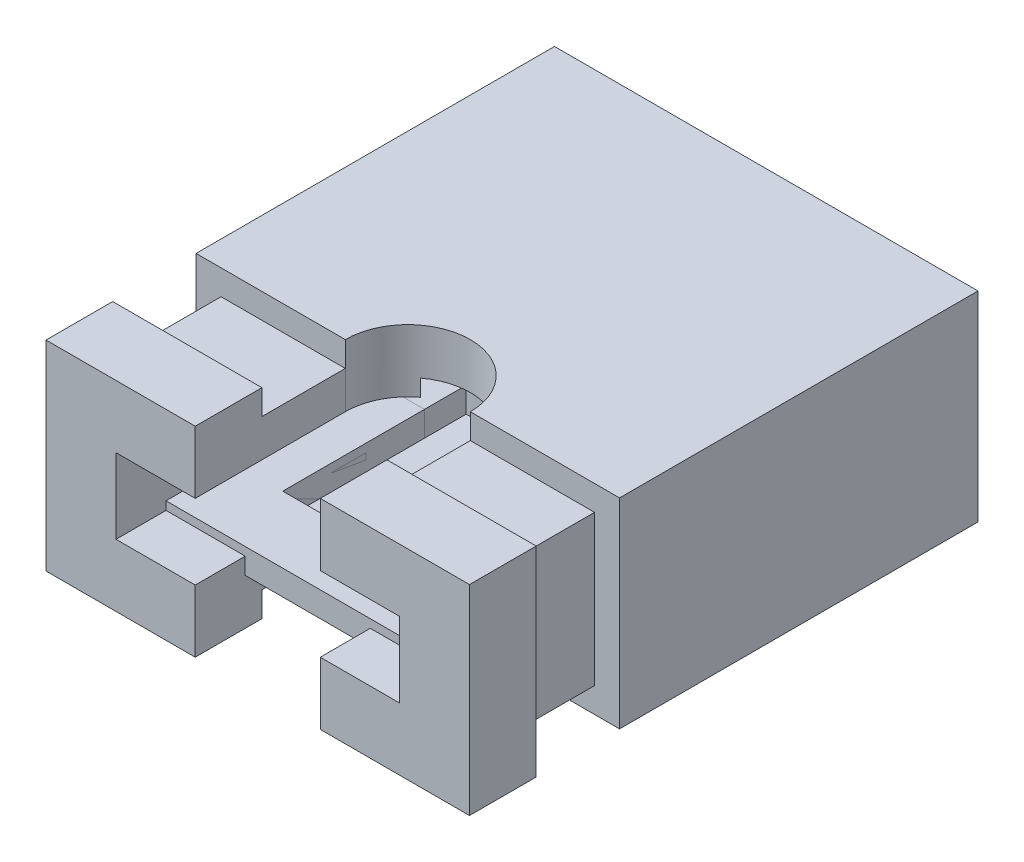
SolidWorks part; units mm, degrees
ref_plane "Front Plane" through (0, 0, 0) normal (0, 0, 1) x (1, 0, 0)
ref_plane "Top Plane" through (0, 0, 0) normal (0, 1, 0) x (1, 0, 0)
ref_plane "Right Plane" through (0, 0, 0) normal (1, 0, 0) x (0, 0, -1)
sketch "Sketch1" plane through (0, 0, 0) normal (0, 0, 1) x (1, 0, 0)
  line L0 (-1.9, 0.65) -> (-1.9, -0.65)
  line L1 (2.54, -1.2) -> (2.54, 1.2)
  line L2 (2.54, 1.2) -> (-2.54, 1.2)
  line L3 (-2.54, 1.2) -> (-2.54, -1.2)
  line L4 (-2.54, -1.2) -> (2.54, -1.2)
  line L5 (-1.9, -0.65) -> (1.9, -0.65)
  line L6 (1.9, 0.65) -> (-1.9, 0.65)
  line L7 (1.9, -0.65) -> (1.9, 0.65)
extrude "Boss-Extrude1" add sketch "Sketch1" along normal blind 4.3
sketch "Sketch3" plane through (0, 1.2, 0) normal (0, 1, 0) x (1, 0, 0)
  line L0 (2.54, -4.3) -> (-2.54, -4.3) construction
  circle A0 centre (0, -4.3) radius 0.75
extrude "Cut-Extrude2" cut sketch "Sketch3" against normal through all
sketch "Sketch6" plane through (0, 0, 4.3) normal (0, 0, 1) x (1, 0, 0)
  line L2 (-0.75, 0.9) -> (-0.75, 0.65)
  line L3 (-0.75, 0.65) -> (-1.9, 0.65)
  line L4 (-2.24, 0.9) -> (-2.24, -1.2)
  line L5 (-0.75, 0.9) -> (-2.24, 0.9)
  line L6 (-2.24, 0.9) -> (-2.24, -0.9)
  line L7 (-0.75, 0.9) -> (-2.24, 0.9)
  line L8 (-1.9, 0.65) -> (-1.9, -0.65)
  line L9 (-1.9, -0.65) -> (-0.75, -0.65)
  line L10 (-0.75, -0.65) -> (-0.75, -0.9)
  line L13 (0, 1.726) -> (0, -1.726) construction
  line L14 (-2.54, -0.9) -> (-0.75, -0.9)
  line L15 (-2.24, -0.9) -> (-0.75, -0.9)
  line L16 (2.24, 0.9) -> (2.24, -0.9)
  line L17 (2.24, -0.9) -> (0.75, -0.9)
  line L18 (1.9, -0.65) -> (0.75, -0.65)
  line L19 (1.9, 0.65) -> (1.9, -0.65)
  line L20 (0.75, 0.65) -> (1.9, 0.65)
  line L21 (0.75, 0.9) -> (0.75, 0.65)
  line L22 (0.75, 0.9) -> (2.24, 0.9)
  line L23 (0.75, -0.65) -> (0.75, -0.9)
  point P18 (0, 0)
  dimension "D1" = 0.3
  dimension "D2" = 0.3
extrude "Boss-Extrude2" add sketch "Sketch6" along normal blind 1
sketch "Sketch7" plane through (0, 0, 5.3) normal (0, 0, 1) x (1, 0, 0)
  line L8 (-0.75, 1.2) -> (-0.75, 0.9) construction
  line L9 (-0.75, 1.2) -> (-0.75, 0.9)
  line L10 (-0.75, -0.65) -> (-1.9, -0.65) construction
  line L11 (-1.9, -0.65) -> (-1.9, 0.65) construction
  line L12 (-1.9, 0.65) -> (-0.75, 0.65) construction
  line L13 (-0.75, -0.65) -> (-1.9, -0.65)
  line L14 (-1.9, -0.65) -> (-1.9, 0.65)
  line L15 (-1.9, 0.65) -> (-0.75, 0.65)
  line L16 (-0.45, -0.35) -> (-1.6, -0.35)
  line L17 (-0.45, -1.2) -> (-0.45, -0.35)
  line L18 (-2.54, -1.2) -> (-0.45, -1.2)
  line L19 (-2.54, 1.2) -> (-2.54, -1.2)
  line L20 (-1.6, -0.35) -> (-1.6, 0.35)
  line L21 (-0.45, 0.35) -> (-0.45, 1.2)
  line L22 (-0.45, 1.2) -> (-2.54, 1.2)
  line L23 (-1.6, 0.35) -> (-0.45, 0.35)
  line L26 (-2.54, -1.2) -> (-0.75, -1.2)
  line L27 (-2.54, 1.2) -> (-2.54, -1.2)
  line L30 (-0.75, 1.2) -> (-2.54, 1.2)
  line L33 (-0.75, -0.9) -> (-0.75, -1.2) construction
  line L35 (-0.75, -0.9) -> (-0.75, -1.2)
  line L36 (-0.75, -0.9) -> (-0.75, -0.65) construction
  line L37 (-0.75, -0.9) -> (-0.75, -0.65)
  line L39 (0.75, -0.9) -> (0.75, -1.2)
  line L40 (0.75, 1.2) -> (0.75, 0.9)
  line L41 (0.75, -0.9) -> (0.75, -0.65)
  line L42 (0.75, 1.2) -> (2.54, 1.2)
  line L43 (2.54, 1.2) -> (2.54, -1.2)
  line L44 (2.54, -1.2) -> (0.75, -1.2)
  line L45 (1.9, 0.65) -> (0.75, 0.65)
  line L46 (1.9, -0.65) -> (1.9, 0.65)
  line L47 (0.75, -0.65) -> (1.9, -0.65)
  line L48 (0.75, 0.9) -> (0.75, 0.65) construction
  line L49 (0.75, 0.9) -> (0.75, 0.65)
  line L50 (-0.75, 0.65) -> (-0.75, 0.9) construction
  line L51 (-0.75, 0.65) -> (-0.75, 0.9)
  point P20 (0, 0)
  dimension "D1" = 0.3
extrude "Boss-Extrude3" add sketch "Sketch7" along normal blind 0.8
sketch "Sketch9" plane through (0, 0, 6.1) normal (0, 0, 1) x (1, 0, 0)
  line L0 (0.75, 0.65) -> (1.9, 0.65) construction
  line L1 (1.9, 0.65) -> (1.9, -0.65) construction
  line L2 (1.9, -0.65) -> (0.75, -0.65) construction
  line L3 (-0.75, -0.65) -> (-1.9, -0.65) construction
  line L4 (-1.9, -0.65) -> (-1.9, 0.65) construction
  line L5 (-1.9, 0.65) -> (-0.75, 0.65) construction
  line L18 (0.75, 0.65) -> (1.9, 0.65)
  line L19 (1.9, 0.65) -> (1.9, -0.65)
  line L20 (1.9, -0.65) -> (0.75, -0.65)
  line L21 (-0.75, -0.65) -> (-1.9, -0.65)
  line L22 (-1.9, -0.65) -> (-1.9, 0.65)
  line L23 (-1.9, 0.65) -> (-0.75, 0.65)
  line L24 (-0.75, -0.45) -> (-1.7, -0.45)
  line L25 (-1.7, -0.45) -> (-1.7, 0.45)
  line L26 (-1.7, 0.45) -> (-0.75, 0.45)
  line L27 (0.75, 0.45) -> (1.7, 0.45)
  line L28 (1.7, 0.45) -> (1.7, -0.45)
  line L29 (1.7, -0.45) -> (0.75, -0.45)
  line L34 (-0.75, 0.65) -> (0.75, 0.65)
  line L35 (0.75, 0.45) -> (-0.75, 0.45)
  line L36 (-0.75, -0.45) -> (0.75, -0.45)
  line L37 (0.75, -0.65) -> (-0.75, -0.65)
  dimension "D1" = 0.2
extrude "Boss-Extrude4" add sketch "Sketch9" against normal blind 2.4
sketch "Sketch10" plane through (0, 0.65, 0) normal (0, 1, 0) x (1, 0, 0)
  line L0 (0.75, -6.1) -> (0.75, -4.3) construction
  line L1 (-0.75, -6.1) -> (-0.75, -4.3) construction
  line L2 (0.75, -6.1) -> (0.75, -4.3)
  line L3 (-0.75, -6.1) -> (-0.75, -4.3)
  line L4 (0.75, -6.1) -> (-0.75, -6.1) construction
  line L5 (0.75, -6.1) -> (-0.75, -6.1)
  arc A0 (0.75, -4.3) -> (0.45, -3.7) centre (0, -4.3) ccw construction
  arc A1 (-0.45, -3.7) -> (-0.75, -4.3) centre (0, -4.3) ccw construction
  arc A2 (0.45, -3.7) -> (-0.45, -3.7) centre (0, -4.3) ccw construction
  arc A3 (0.75, -4.3) -> (0.45, -3.7) centre (0, -4.3) ccw
  arc A4 (-0.45, -3.7) -> (-0.75, -4.3) centre (0, -4.3) ccw
  arc A5 (0.45, -3.7) -> (-0.45, -3.7) centre (0, -4.3) ccw
extrude "Cut-Extrude4" cut sketch "Sketch10" against normal through all
sketch "Sketch12" plane through (0, 0, 0) normal (0, 0, -1) x (-1, 0, 0)
  line L0 (1.9, 0.65) -> (1.9, -0.65) construction
  line L1 (1.9, -0.65) -> (-1.9, -0.65) construction
  line L2 (-1.9, -0.65) -> (-1.9, 0.65) construction
  line L3 (1.9, 0.65) -> (1.9, -0.65)
  line L4 (1.9, -0.65) -> (-1.9, -0.65)
  line L5 (-1.9, -0.65) -> (-1.9, 0.65)
  line L6 (1.6, 0.65) -> (1.6, -0.35)
  line L7 (1.6, -0.35) -> (-1.6, -0.35)
  line L8 (-1.6, -0.35) -> (-1.6, 0.65)
  line L9 (-1.9, 0.65) -> (-1.6, 0.65)
  line L10 (1.6, 0.65) -> (1.9, 0.65)
  dimension "D1" = 0.3
extrude "Boss-Extrude5" add sketch "Sketch12" against normal blind 3 separate body
sketch "Sketch13" plane through (0, 0, 3) normal (0, 0, 1) x (1, 0, 0)
  line L0 (1.9, -0.65) -> (-1.9, -0.65) construction
  line L1 (-1.6, -0.35) -> (1.6, -0.35) construction
  line L2 (1.9, -0.65) -> (-1.9, -0.65)
  line L3 (-1.6, -0.35) -> (1.6, -0.35)
  line L4 (-1.6, -0.35) -> (-1.9, -0.35)
  line L5 (-1.9, -0.65) -> (-1.9, 0.65) construction
  line L6 (-1.9, -0.35) -> (-1.9, -0.65)
  line L7 (1.6, -0.35) -> (1.9, -0.35)
  line L8 (1.9, 0.65) -> (1.9, -0.65) construction
  line L9 (1.9, -0.35) -> (1.9, -0.65)
extrude "Boss-Extrude8" add sketch "Sketch13" along normal blind 2.5 separate body
sketch "Sketch14" plane through (0, -0.35, 0) normal (0, 1, 0) x (1, 0, 0)
  line L22 (1.1, -2.5) -> (-1.1, -2.5)
  line L23 (-1.1, -2.5) -> (-1.1, -4.7)
  line L24 (-1.1, -4.7) -> (1.1, -4.7)
  line L25 (1.1, -4.7) -> (1.1, -2.5)
extrude "Cut-Extrude5" cut sketch "Sketch14" against normal blind 0.3
